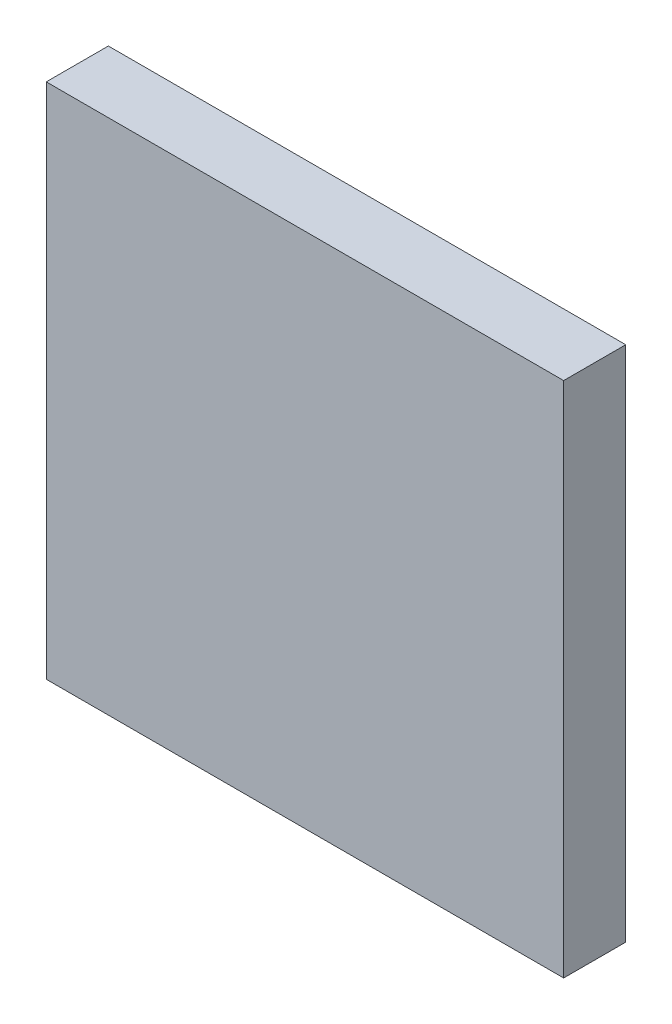
SolidWorks part; units mm, degrees
material "Glass"
ref_plane "Front Plane" through (0, 0, 0) normal (0, 0, 1) x (1, 0, 0)
ref_plane "Top Plane" through (0, 0, 0) normal (0, 1, 0) x (1, 0, 0)
ref_plane "Right Plane" through (0, 0, 0) normal (1, 0, 0) x (0, 0, -1)
sketch "Sketch1" plane through (0, 0, 0) normal (0, 0, 1) x (1, 0, 0)
  line L1 (-12.5, 12.5) -> (12.5, 12.5)
  line L2 (-12.5, 12.5) -> (-12.5, -12.5)
  line L3 (-12.5, -12.5) -> (12.5, -12.5)
  line L4 (12.5, 12.5) -> (12.5, -12.5)
  line L5 (-12.5, 12.5) -> (12.5, -12.5) construction
  line L6 (-12.5, -12.5) -> (12.5, 12.5) construction
  point P0 (0, 0)
  dimension "D1" = 25
extrude "Boss-Extrude1" add sketch "Sketch1" along normal blind 3
